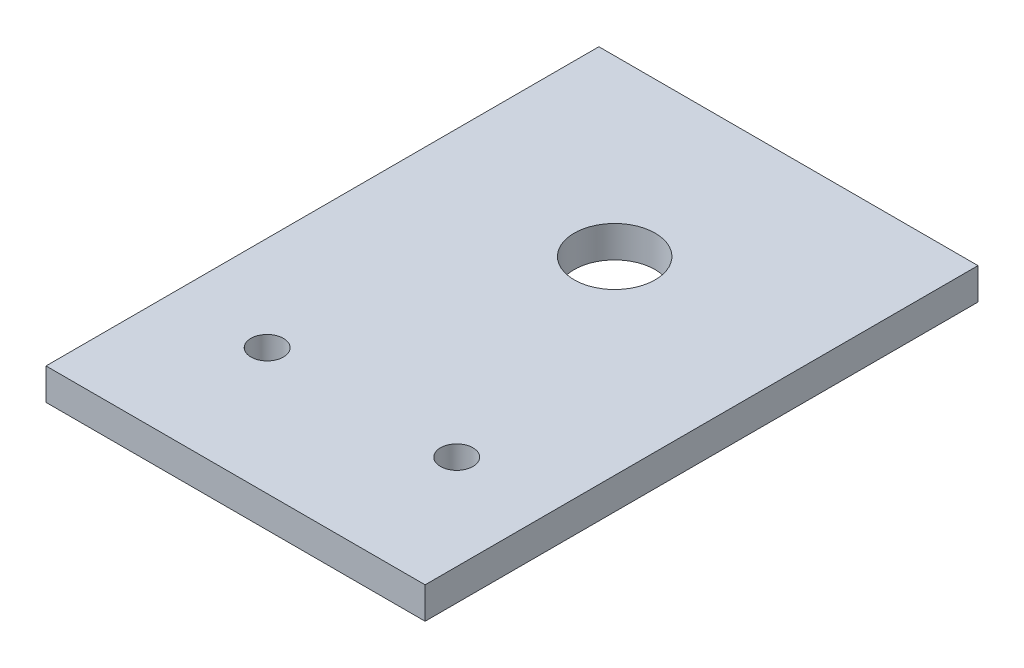
SolidWorks part; units mm, degrees
ref_plane "Front Plane" through (0, 0, 0) normal (0, 0, 1) x (1, 0, 0)
ref_plane "Top Plane" through (0, 0, 0) normal (0, 1, 0) x (1, 0, 0)
ref_plane "Right Plane" through (0, 0, 0) normal (1, 0, 0) x (0, 0, -1)
sketch "Sketch1" plane through (0, 0, 0) normal (0, 1, 0) x (1, 0, 0)
  line L1 (-38.1, -55.5625) -> (38.1, -55.5625)
  line L2 (-38.1, -55.5625) -> (-38.1, 55.5625)
  line L3 (-38.1, 55.5625) -> (38.1, 55.5625)
  line L4 (38.1, -55.5625) -> (38.1, 55.5625)
  line L5 (-38.1, -55.5625) -> (38.1, 55.5625) construction
  line L6 (-38.1, 55.5625) -> (38.1, -55.5625) construction
  point P0 (0, 0)
  dimension "D1" = 76.2
  dimension "D2" = 111.125
extrude "Boss-Extrude1" add sketch "Sketch1" along normal blind 6.35
sketch "Sketch2" plane through (0, 0, 0) normal (0, -1, 0) x (-1, 0, 0)
  line L0 (0, -55.5625) -> (0, 55.5625) construction
  line L1 (38.1, -55.5625) -> (-38.1, -55.5625) construction
  line L2 (-38.1, 55.5625) -> (38.1, 55.5625) construction
  circle A0 centre (-19.05, -30.1625) radius 3.2639
  circle A1 centre (19.05, -30.1625) radius 3.2639
  circle A2 centre (0, 20.6375) radius 8.1356
  dimension "D1" = 19.05
  dimension "D3" = 6.5278
  dimension "D4" = 16.2712
  dimension "D2" = 25.4
  dimension "D5" = 34.925
extrude "Cut-Extrude1" cut sketch "Sketch2" against normal through all
